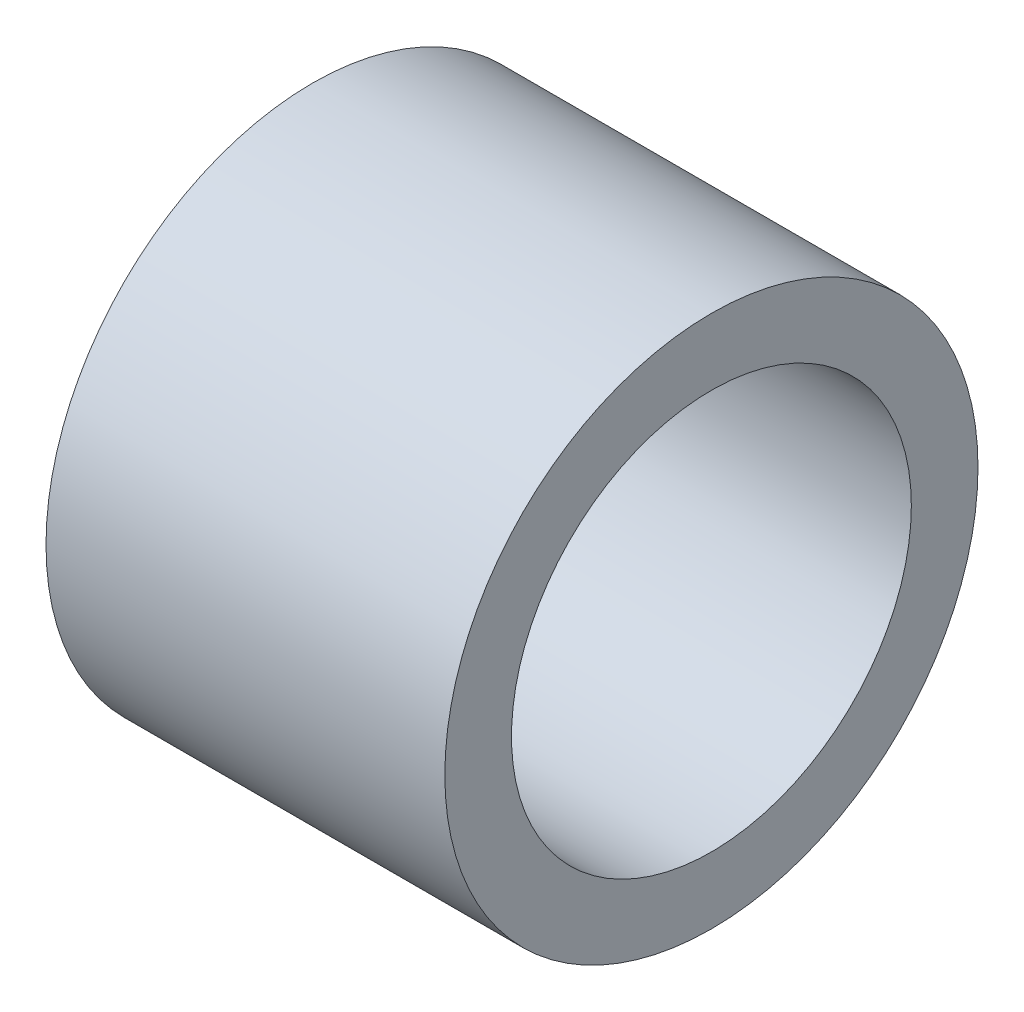
SolidWorks part; units mm, degrees
ref_plane "Front Plane" through (0, 0, 0) normal (0, 0, 1) x (1, 0, 0)
ref_plane "Top Plane" through (0, 0, 0) normal (0, 1, 0) x (1, 0, 0)
ref_plane "Right Plane" through (0, 0, 0) normal (1, 0, 0) x (0, 0, -1)
sketch "Sketch1" plane through (0, 0, 0) normal (1, 0, 0) x (0, 0, -1)
  circle A0 centre (0, 0) radius 9.525
  circle A1 centre (0, 0) radius 12.7
  dimension "D1" = 25.4
  dimension "D2" = 19.05
extrude "Boss-Extrude1" add sketch "Sketch1" against normal mid plane 19
